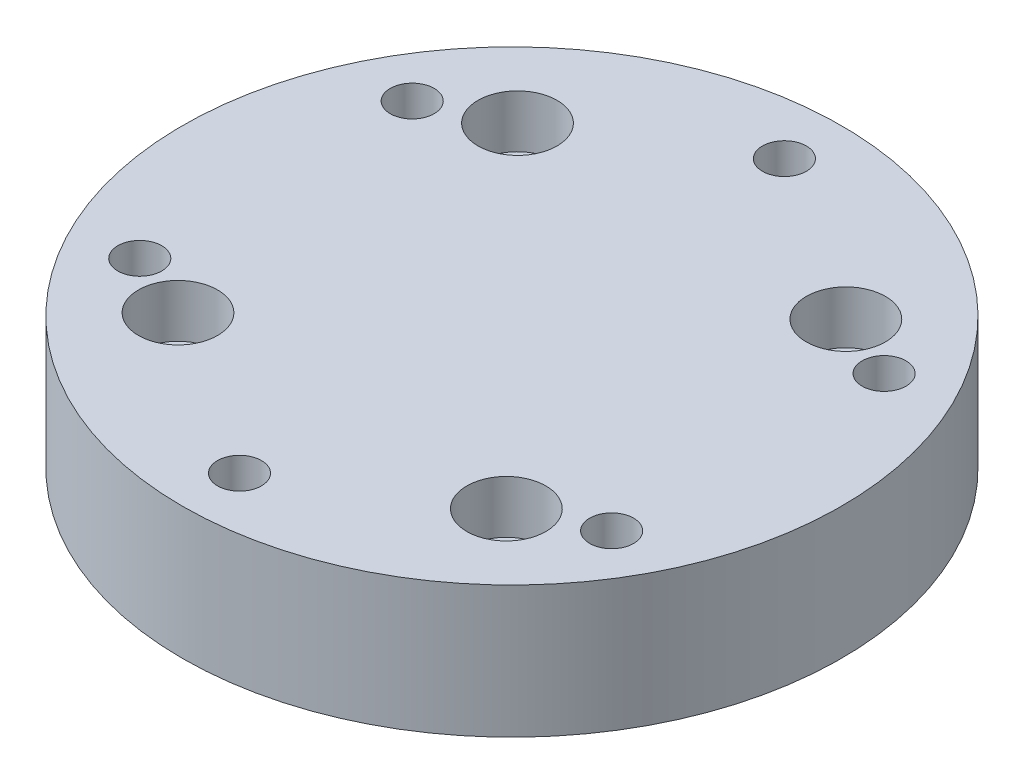
SolidWorks part; units mm, degrees
material "7075-T6 (SN)"
ref_plane "Front Plane" through (0, 0, 0) normal (0, 0, 1) x (1, 0, 0)
ref_plane "Top Plane" through (0, 0, 0) normal (0, 1, 0) x (1, 0, 0)
ref_plane "Right Plane" through (0, 0, 0) normal (1, 0, 0) x (0, 0, -1)
sketch "Sketch2" plane through (0, 0, 0) normal (0, 1, 0) x (1, 0, 0)
  circle A0 centre (0, 0) radius 37.5
  circle A2 centre (0, 0) radius 26.87 construction
  circle A10 centre (-18.6792, 19.3154) radius 2.5
  circle A11 centre (19.3154, 18.6792) radius 2.5
  circle A12 centre (18.6792, -19.3154) radius 2.5
  circle A13 centre (-19.3154, -18.6792) radius 2.5
  point P5 (0, 31)
  point P10 (26.8468, 15.5)
  point P11 (26.8468, -15.5)
  point P12 (0, -31)
  point P13 (-26.8468, -15.5)
  point P14 (-26.8468, 15.5)
  dimension "D1" = 75
  dimension "D3" = 53.7401
  dimension "D4" = 6
  dimension "D6" = 5
  dimension "D7" = 4
extrude "Boss-Extrude1" add sketch "Sketch2" along normal blind 15
sketch "Sketch3" plane through (0, 15, 0) normal (0, 1, 0) x (1, 0, 0)
  circle A0 centre (-18.6792, 19.3154) radius 4.5
  circle A1 centre (19.3154, 18.6792) radius 4.5
  circle A2 centre (18.6792, -19.3154) radius 4.5
  circle A3 centre (-19.3154, -18.6792) radius 4.5
  dimension "D1" = 9
  dimension "D2" = 4
extrude "Cut-Extrude1" cut sketch "Sketch3" against normal blind 6
sketch "Sketch12" plane through (0, 15, 0) normal (0, 1, 0) x (1, 0, 0)
  circle A0 centre (0, 0) radius 31 construction
  point P3 (0, 31)
  point P6 (26.8468, 15.5)
  point P7 (26.8468, -15.5)
  point P8 (0, -31)
  point P9 (-26.8468, -15.5)
  point P10 (-26.8468, 15.5)
  dimension "D1" = 62
  dimension "D2" = 6
hole_wizard "M6x1.0 Tapped Hole1" positions "3DSketch7" profile "Sketch14" tap size "M6x1.0" standard "ANSI Metric" end condition through all
sketch3d "3DSketch7"
  point P0 (0, 15, -31)
  point P3 (26.8468, 15, -15.5)
  point P6 (26.8468, 15, 15.5)
  point P9 (0, 15, 31)
  point P12 (-26.8468, 15, 15.5)
  point P15 (-26.8468, 15, -15.5)
sketch "Sketch14" plane through (0, 15, -31) normal (1, 0, 0) x (0, 0, 1)
  line L0 (0, 0) -> (0, 15)
  line L1 (0, 15) -> (2.5, 15)
  line L2 (2.5, 15) -> (2.5, 0)
  line L5 (2.5, 0) -> (0, 0)
  line L11 (0, -6.35) -> (0, 107.95) construction
  dimension "Thru Tap Drill Dia." = 5
  dimension "Thru Tap Drill Depth" = 15
cosmetic thread "Hole Thread1" parameters "D2"=6
cosmetic thread "Hole Thread2" parameters "D2"=6
cosmetic thread "Hole Thread3" parameters "D2"=6
cosmetic thread "Hole Thread4" parameters "D2"=6
cosmetic thread "Hole Thread5" parameters "D2"=6
cosmetic thread "Hole Thread6" parameters "D2"=6
